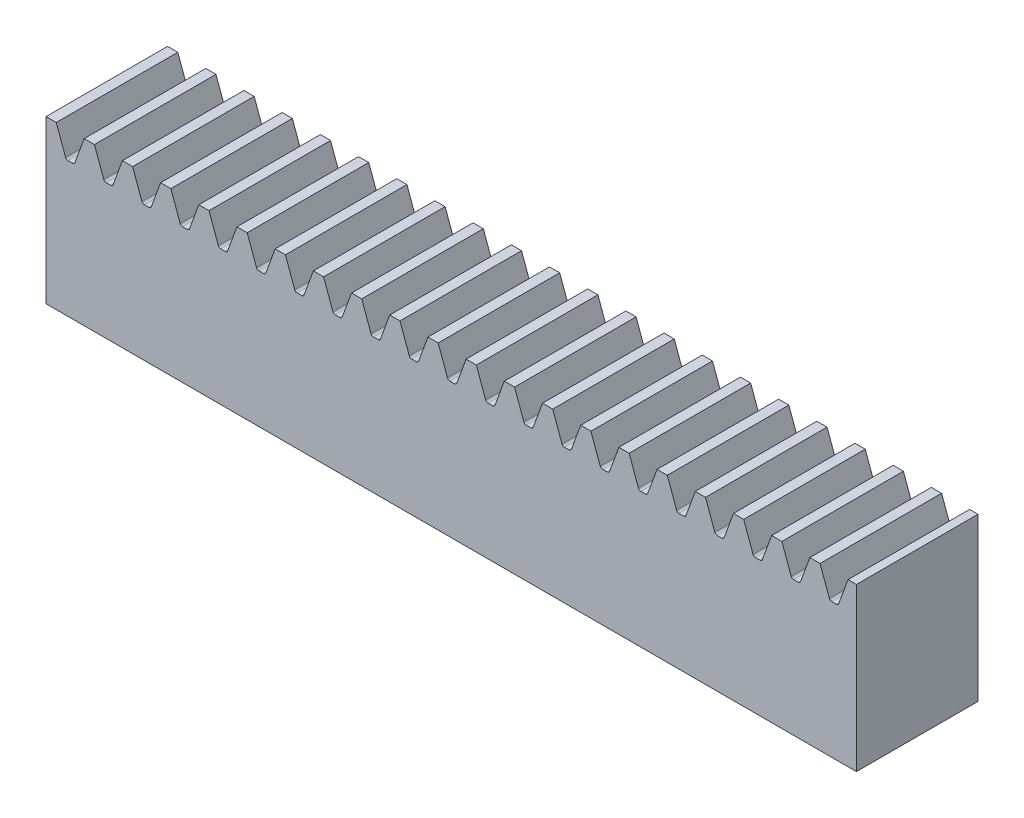
SolidWorks part; units mm, degrees
ref_plane "Front Plane" through (0, 0, 0) normal (0, 0, 1) x (1, 0, 0)
ref_plane "Top Plane" through (0, 0, 0) normal (0, 1, 0) x (1, 0, 0)
ref_plane "Right Plane" through (0, 0, 0) normal (1, 0, 0) x (0, 0, -1)
sketch "Sketch1" plane through (0, 0, 0) normal (0, 0, 1) x (1, 0, 0)
  line L0 (0, 0) -> (-50, 0) construction
  line L1 (0, 0) -> (50, 0) construction
  line L2 (0, 0) -> (0, 20) construction
  line L3 (-50, 18.5) -> (50, 18.5) construction
  point P3 (380.1067, 0)
  point P7 (0, 20)
sketch "Sketch2" plane through (0, 0, 0) normal (1, 0, 0) x (0, 0, -1)
  line L0 (0, 0) -> (0, 20) construction
  line L1 (7.5, 20) -> (-7.5, 20)
  line L2 (0, 10) -> (-7.5, 10) construction
  line L3 (0, 10) -> (7.5, 10) construction
  line L4 (-7.5, 20) -> (-7.5, 0)
  line L5 (-7.5, 0) -> (7.5, 0)
  line L6 (7.5, 0) -> (7.5, 20)
  dimension "Width" = 15
extrude "Boss-Extrude1" add sketch "Sketch2" along normal up to vertex (50 mm away) and the other way up to vertex (50 mm away) up to point (50, 0, 0) other way up to point (-50, 0, 0)
sketch "Sketch3" plane through (0, 0, 0) normal (0, 0, 1) x (1, 0, 0)
  line L0 (-48.7357, 20) -> (-47.5161, 16.6492)
  line L2 (-47.5161, 16.6492) -> (-46.5072, 16.6492)
  line L3 (-46.5072, 16.6492) -> (-45.2876, 20)
  line L4 (-48.7357, 20) -> (-45.2876, 20)
  line L5 (-48.7357, 20) -> (-50, 20) construction
  line L6 (-45.2876, 20) -> (-44.0233, 20) construction
  line L7 (-44.0233, 20) -> (-42.8037, 16.6492) construction
  line L8 (-47.0117, 16.6492) -> (-47.0117, 20) construction
  line L9 (-48.1898, 18.5) -> (-45.8336, 18.5) construction
  line L10 (-45.8336, 18.5) -> (-45.8336, 20) construction
  line L11 (-43.4774, 18.5) -> (-43.4774, 16.6492) construction
  line L12 (-45.8336, 18.5) -> (-43.4774, 18.5) construction
  line L13 (-50, 20) -> (-50, 0) construction
  line L14 (50, 20) -> (-50, 20) construction
  dimension "D1" = 20
  dimension "D2" = 20
  dimension "D3" = 3.3508
  dimension "D4" = 1.5
  dimension "D5" = 4.7124
  dimension "D6" = 1.0089
  dimension "D7" = 1.2643
extrude "Cut-Extrude1" cut sketch "Sketch3" against normal through all both and the other way through all
fillet "Fillet1" radius 0.3027 2 edges at (-46.5072, 16.6492, 0) (-47.5161, 16.6492, 0)
pattern_linear "LPattern1" count 21 spacing 4.7124 along (1, 0, 0) of "Cut-Extrude1", "Fillet1"
equation "\"D3@Sketch3\"=(2.2/\"Diametral Pitch@Sketch1\")+.002"
equation "\"D4@Sketch3\"=1/\"Diametral Pitch@Sketch1\""
equation "\"D5@Sketch3\"=3.1416/\"Diametral Pitch@Sketch1\""
equation "\"D1@Fillet1\"=\"D6@Sketch3\"*.3"
equation "\"D3@LPattern1\"=\"D5@Sketch3\""
equation "\"D1@LPattern1\"=\"Overall Length@Sketch1\"*11"
